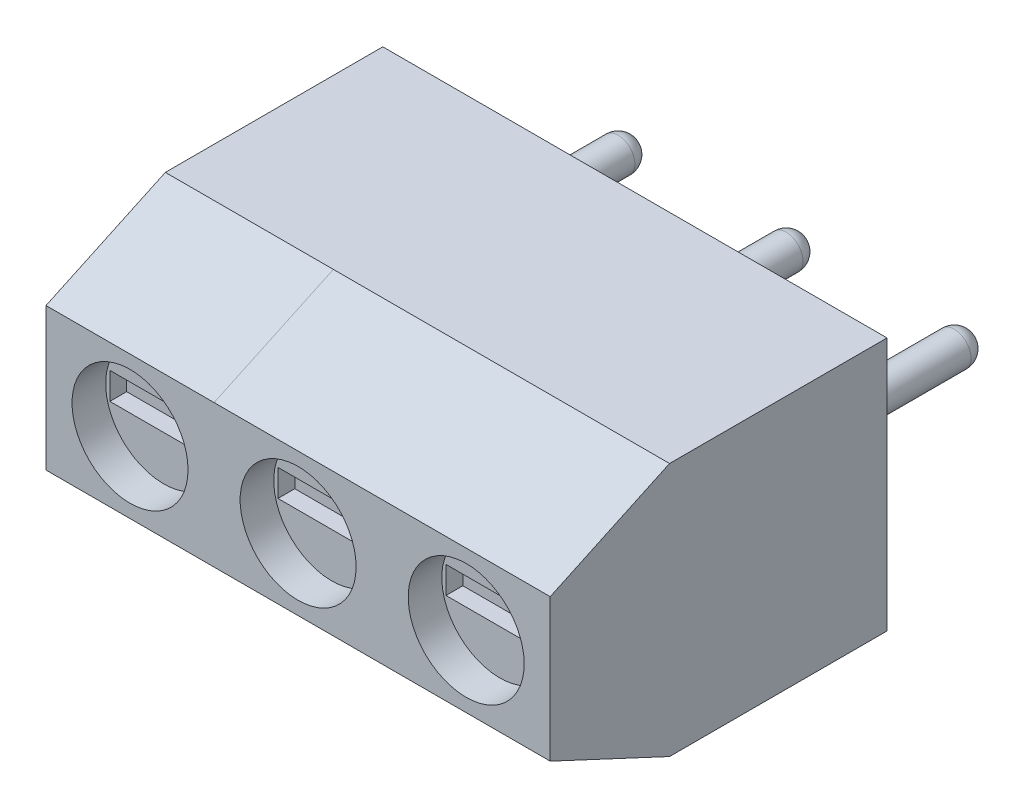
SolidWorks part; units mm, degrees
ref_plane "Face" through (0, 0, 0) normal (0, 0, 1) x (1, 0, 0)
ref_plane "Dessus" through (0, 0, 0) normal (0, 1, 0) x (1, 0, 0)
ref_plane "Droite" through (0, 0, 0) normal (1, 0, 0) x (0, 0, -1)
sketch "Esquisse1" plane through (0, 0, 0) normal (0, 0, 1) x (1, 0, 0)
  line L1 (0, 0) -> (5, 0)
  line L2 (0, 0) -> (0, 7.55)
  line L3 (0, 7.55) -> (5, 7.55)
  line L4 (5, 0) -> (5, 7.55)
  dimension "D1" = 5
  dimension "D2" = 7.55
extrude "Extrusion1" add sketch "Esquisse1" along normal blind 10.02
chamfer "Chanfrein1" distance 3.55 angle 25 2 edges at (2.5, 7.55, 10.02) (2.5, 0, 10.02)
sketch "Esquisse2" plane through (0, 0, 10.02) normal (0, 0, 1) x (1, 0, 0)
  line L0 (0, 3.775) -> (5, 3.775) construction
  line L1 (0, 5.8946) -> (0, 1.6554) construction
  line L2 (5, 1.6554) -> (5, 5.8946) construction
  line L3 (2.5, 5.8946) -> (2.5, 1.6554) construction
  line L4 (5, 5.8946) -> (0, 5.8946) construction
  line L5 (0, 1.6554) -> (5, 1.6554) construction
  circle A1 centre (2.5, 3.775) radius 1.725
extrude "Enlèv. mat.-Extru.1" cut sketch "Esquisse2" against normal blind 1
sketch "Esquisse3" plane through (0, 0, 0) normal (0, -1, 0) x (1, 0, 0)
  line L0 (0, 0) -> (5, 0) construction
  line L3 (0, 6.47) -> (0, 0) construction
  line L4 (4.5, 5.8) -> (0.5, 5.8)
  line L5 (4.5, 5.8) -> (4.5, 0.8)
  line L6 (4.5, 0.8) -> (0.5, 0.8)
  line L7 (0.5, 5.8) -> (0.5, 0.8)
  dimension "D1" = 5
  dimension "D2" = 4
  dimension "D3" = 0.8
  dimension "D4" = 0.5
extrude "Enlèv. mat.-Extru.2" cut sketch "Esquisse3" against normal blind 1.6
sketch "Esquisse4" plane through (0, 1.6, 0) normal (0, -1, 0) x (1, 0, 0)
  line L0 (5.937, 0.8) -> (-1.7318, 0.8) construction
  line L3 (5.937, 3.3) -> (-1.7318, 3.3) construction
  line L6 (2.5, -1.3707) -> (2.5, 11.1286) construction
  line L9 (0, -1.9984) -> (0, 11.8381) construction
  circle A1 centre (2.5, 3.3) radius 1.675
  dimension "D1" = 2.5
  dimension "D2" = 2.5
extrude "Enlèv. mat.-Extru.3" cut sketch "Esquisse4" against normal blind 1.6
sketch "Esquisse5" plane through (0, 0, 0) normal (0, 0, -1) x (-1, 0, 0)
  line L0 (-5, 3.775) -> (0, 3.775) construction
  line L1 (-5, 0) -> (-5, 7.55) construction
  line L2 (0, 7.55) -> (0, 0) construction
  line L3 (-2.5, 7.55) -> (-2.5, 0) construction
  line L4 (-5, 7.55) -> (0, 7.55) construction
  line L5 (0, 0) -> (-5, 0) construction
  circle A0 centre (-2.5, 3.775) radius 0.5
extrude "Extrusion2" add sketch "Esquisse5" along normal blind 5
fillet "Congé1" radius 0.5 1 edges at (2, 3.775, -5)
sketch "Esquisse6" plane through (0, 0, 9.02) normal (0, 0, 1) x (1, 0, 0)
  line L0 (-0.6376, 3.775) -> (5.8647, 3.775) construction
  line L1 (2.5, 5.2292) -> (2.5, 3.3641) construction
  line L2 (-0.5728, 3.375) -> (6.7721, 3.375) construction
  line L3 (-0.6376, 4.175) -> (6.7721, 4.175) construction
  line L4 (0.9, 5.5892) -> (0.9, 2.5433) construction
  line L5 (4.1, 5.5892) -> (4.1, 2.2696) construction
  line L7 (0.9, 4.175) -> (4.1, 4.175)
  line L8 (0.9, 4.175) -> (0.9, 3.375)
  line L9 (0.9, 3.375) -> (4.1, 3.375)
  line L10 (4.1, 4.175) -> (4.1, 3.375)
  dimension "D1" = 0.4
  dimension "D2" = 0.8
  dimension "D3" = 1.6
  dimension "D4" = 3.2
extrude "Enlèv. mat.-Extru.4" cut sketch "Esquisse6" against normal blind 0.5
pattern_linear "Répétition linéaire5" count 3 spacing 5 along (1, 0, 0) of "Extrusion1", "Enlèv. mat.-Extru.1", "Enlèv. mat.-Extru.2", "Enlèv. mat.-Extru.3", "Extrusion2", "Congé1", "Enlèv. mat.-Extru.4"
chamfer "Chanfrein2" distance 3.55 angle 25 1 edges at (10, 0, 10.02)
